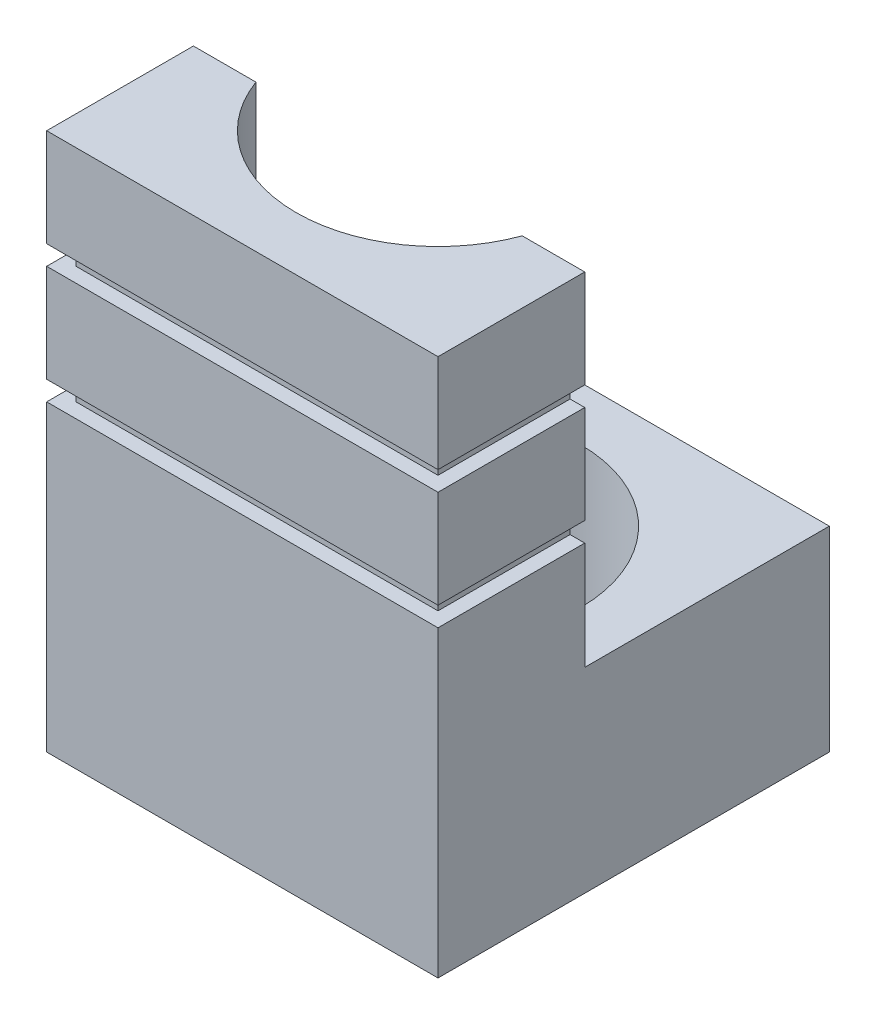
SolidWorks part; units mm, degrees
ref_plane "Plane1" through (0, 0, 0) normal (0, 0, 1) x (1, 0, 0)
ref_plane "Plane2" through (0, 0, 0) normal (0, 1, 0) x (1, 0, 0)
ref_plane "Plane3" through (0, 0, 0) normal (1, 0, 0) x (0, 0, -1)
sketch "Sketch4" plane through (0, 0, 0) normal (1, 0, 0) x (0, 0, -1)
  line L0 (0, 0) -> (80, 0)
  line L1 (80, 0) -> (80, 40)
  line L2 (80, 40) -> (30, 40)
  line L3 (30, 40) -> (30, 110)
  line L4 (30, 110) -> (0, 110)
  line L5 (0, 110) -> (0, 0)
  point P3 (21.2105, 36.6053)
  dimension "D1" = 80
  dimension "D2" = 110
  dimension "D3" = 40
  dimension "D4" = 30
extrude "Boss-Extrude2" add sketch "Sketch4" along normal blind 80
sketch "Sketch5" plane through (0, 110, 0) normal (0, 1, 0) x (1, 0, 0)
  line L1 (80, 30) -> (80, 0) construction
  line L4 (80, 0) -> (0, 0) construction
  circle A0 centre (40, 40) radius 29
  point P6 (0, 0)
  dimension "D1" = 58
  dimension "D2" = 40
  dimension "D3" = 40
extrude "Cut-Extrude1" cut sketch "Sketch5" against normal blind 100
sketch "Sketch6" plane through (0, 0, 0) normal (0, -1, 0) x (1, 0, 0)
  line L0 (80, -80) -> (0, 0) construction
  line L1 (0, -80) -> (80, 0) construction
  circle A0 centre (40, -40) radius 24
  point P10 (0, 0)
  point P11 (40, -40)
  dimension "D1" = 48
extrude "Cut-Extrude2" cut sketch "Sketch6" against normal through all
sketch "Sketch7" plane through (80, 0, 0) normal (1, 0, 0) x (0, 0, -1)
  line L0 (0, 90) -> (30, 90)
  line L1 (0, 110) -> (0, 0) construction
  line L2 (30, 40) -> (30, 110) construction
  line L3 (0, 86) -> (30, 86)
  line L4 (0, 66) -> (30, 66)
  line L5 (0, 62) -> (30, 62)
  line L6 (0, 90) -> (0, 86)
  line L7 (30, 90) -> (30, 86)
  line L8 (0, 66) -> (0, 62)
  line L9 (30, 66) -> (30, 62)
  line L10 (30, 110) -> (0, 110) construction
  dimension "D1" = 4
  dimension "D2" = 4
  dimension "D3" = 20
  dimension "D4" = 20
extrude "Cut-Extrude3" cut sketch "Sketch7" against normal blind 3
sketch "Sketch8" plane through (0, 0, 0) normal (-1, 0, 0) x (0, 0, 1)
  line L0 (-30, 90) -> (0, 90)
  line L1 (-30, 40) -> (-30, 110) construction
  line L2 (0, 110) -> (0, 0) construction
  line L3 (0, 86) -> (-30, 86)
  line L4 (-30, 90) -> (-30, 86)
  line L5 (0, 90) -> (0, 86)
  line L6 (-30, 110) -> (0, 110) construction
  line L7 (-30, 66) -> (0, 66)
  line L8 (-30, 66) -> (-30, 62)
  line L9 (-30, 62) -> (0, 62)
  line L10 (0, 66) -> (0, 62)
  dimension "D1" = 4
  dimension "D2" = 4
  dimension "D3" = 20
  dimension "D4" = 20
extrude "Cut-Extrude4" cut sketch "Sketch8" against normal blind 3
sketch "Sketch9" plane through (0, 0, 0) normal (0, 0, 1) x (1, 0, 0)
  line L1 (3, 90) -> (77, 90)
  line L2 (3, 90) -> (3, 86)
  line L3 (3, 86) -> (77, 86)
  line L4 (77, 90) -> (77, 86)
  line L5 (3, 66) -> (77, 66)
  line L6 (3, 66) -> (3, 62)
  line L7 (3, 62) -> (77, 62)
  line L8 (77, 66) -> (77, 62)
extrude "Cut-Extrude5" cut sketch "Sketch9" against normal blind 3
